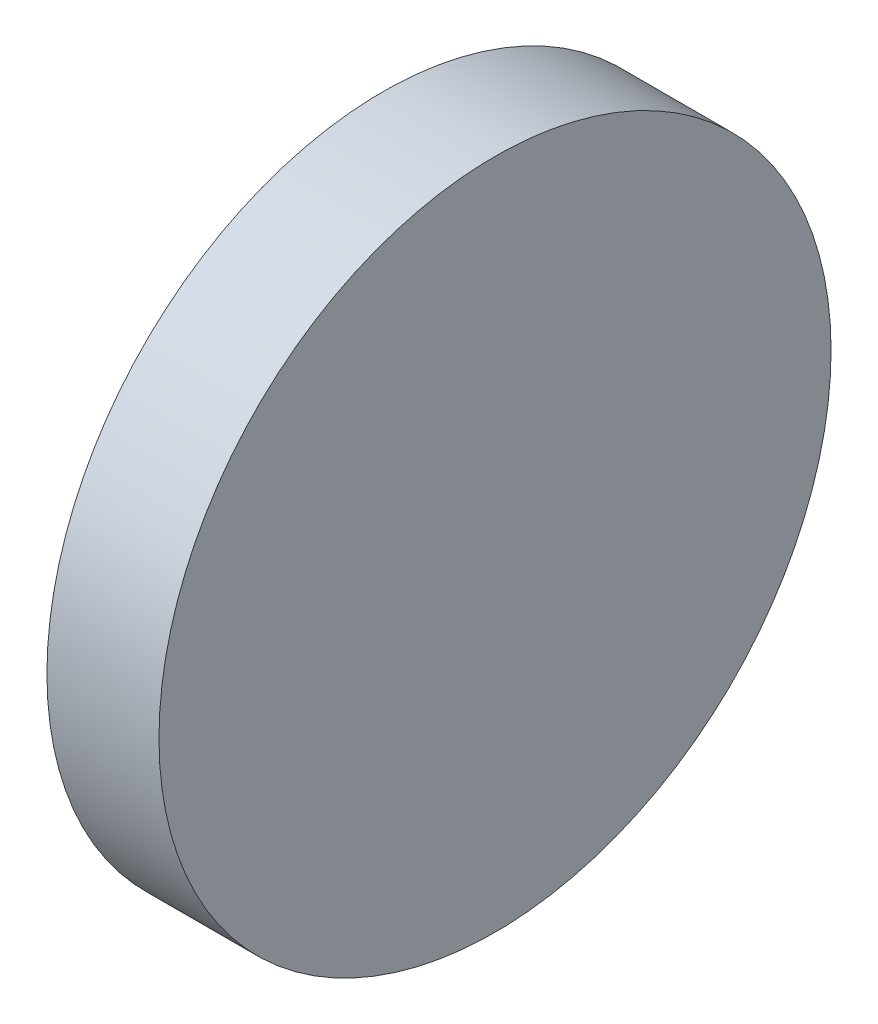
SolidWorks part; units mm, degrees
ref_plane "Front" through (0, 0, 0) normal (0, 0, 1) x (1, 0, 0)
ref_plane "Top" through (0, 0, 0) normal (0, 1, 0) x (1, 0, 0)
ref_plane "Right" through (0, 0, 0) normal (1, 0, 0) x (0, 0, -1)
sketch "Sketch1" plane through (0, 0, 0) normal (1, 0, 0) x (0, 0, -1)
  circle A0 centre (0, 0) radius 15
  dimension "D1" = 30
extrude "Boss-Extrude1" add sketch "Sketch1" along normal blind 5
